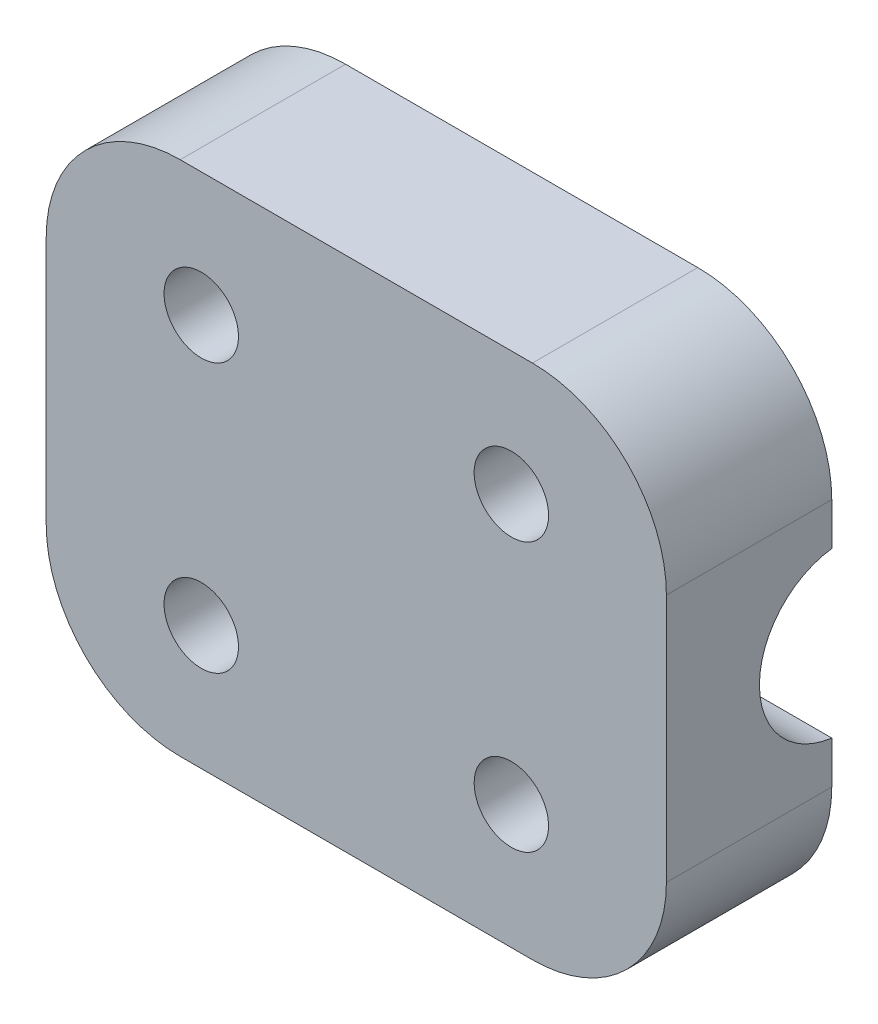
SolidWorks part; units mm, degrees
ref_plane "Front Plane" through (0, 0, 0) normal (0, 0, 1) x (1, 0, 0)
ref_plane "Top Plane" through (0, 0, 0) normal (0, 1, 0) x (1, 0, 0)
ref_plane "Right Plane" through (0, 0, 0) normal (1, 0, 0) x (0, 0, -1)
sketch "Sketch1" plane through (0, 0, 0) normal (0, 0, 1) x (1, 0, 0)
  line L7 (8.5192, 26.5) -> (-8.5192, 26.5)
  line L9 (-15, 20.0192) -> (-15, 7.9808)
  line L11 (-8.5192, 1.5) -> (8.5192, 1.5)
  line L13 (15, 7.9808) -> (15, 20.0192)
  line L37 (0, 26.5) -> (0, 1.5) construction
  line L39 (15, 14) -> (-15, 14) construction
  circle A0 centre (7.5, 20.5) radius 1.8
  circle A1 centre (-7.5, 20.5) radius 1.8
  circle A2 centre (-7.5, 7.5) radius 1.8
  circle A3 centre (7.5, 7.5) radius 1.8
  arc A5 (-15, 20.0192) -> (-8.5192, 26.5) centre (-8.5192, 20.0192) cw
  arc A6 (-15, 7.9808) -> (-8.5192, 1.5) centre (-8.5192, 7.9808) ccw
  arc A7 (15, 7.9808) -> (8.5192, 1.5) centre (8.5192, 7.9808) cw
  arc A8 (15, 20.0192) -> (8.5192, 26.5) centre (8.5192, 20.0192) ccw
extrude "Boss-Extrude1" add sketch "Sketch1" against normal blind 8
sketch "Sketch2" plane through (-15, 0, 0) normal (-1, 0, 0) x (0, 0, 1)
  circle A0 centre (-8.5, 14) radius 3.5
extrude "Cut-Extrude1" cut sketch "Sketch2" against normal through all
sketch "Sketch3" plane through (15, 0, 0) normal (1, 0, 0) x (0, 0, -1)
  circle A0 centre (8.5, 14) radius 4
extrude "Cut-Extrude2" cut sketch "Sketch3" against normal blind 15
